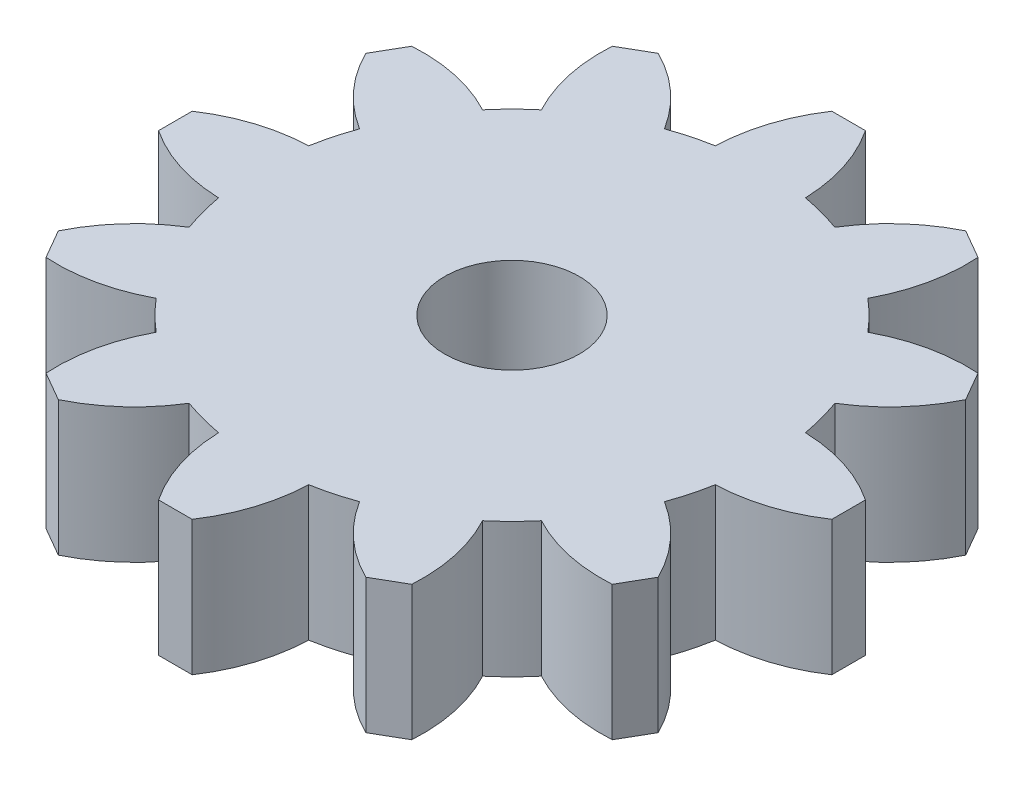
SolidWorks part; units mm, degrees
ref_plane "Front Plane" through (0, 0, 0) normal (0, 0, 1) x (1, 0, 0)
ref_plane "Top Plane" through (0, 0, 0) normal (0, 1, 0) x (1, 0, 0)
ref_plane "Right Plane" through (0, 0, 0) normal (1, 0, 0) x (0, 0, -1)
sketch "Sketch1" plane through (0, 0, 0) normal (0, 1, 0) x (1, 0, 0)
  line L0 (0, 0) -> (0, 18.9151) construction
  line L1 (-1, 20) -> (1, 20)
  line L2 (9.134, 17.8205) -> (10.866, 16.8205)
  line L3 (16.8205, 10.866) -> (17.8205, 9.134)
  line L4 (20, 1) -> (20, -1)
  line L5 (17.8205, -9.134) -> (16.8205, -10.866)
  line L6 (10.866, -16.8205) -> (9.134, -17.8205)
  line L7 (1, -20) -> (-1, -20)
  line L8 (-9.134, -17.8205) -> (-10.866, -16.8205)
  line L9 (-16.8205, -10.866) -> (-17.8205, -9.134)
  line L10 (-20, -1) -> (-20, 1)
  line L11 (-17.8205, 9.134) -> (-16.8205, 10.866)
  line L12 (-10.866, 16.8205) -> (-9.134, 17.8205)
  circle A0 centre (0, 0) radius 4
  arc A1 (-2.675, 14.7596) -> (-5.0632, 14.1196) centre (0, 0) ccw
  arc A2 (-1, 20) -> (-2.675, 14.7596) centre (7.3203, 14.4527) ccw
  arc A3 (1, 20) -> (2.675, 14.7596) centre (-7.3203, 14.4527) cw
  arc A4 (10.866, 16.8205) -> (9.6964, 11.4446) centre (0.8868, 16.1765) cw
  arc A5 (9.134, 17.8205) -> (5.0632, 14.1196) centre (13.5659, 8.8562) ccw
  arc A6 (17.8205, 9.134) -> (14.1196, 5.0632) centre (8.8562, 13.5659) cw
  arc A7 (16.8205, 10.866) -> (11.4446, 9.6964) centre (16.1765, 0.8868) ccw
  arc A8 (20, -1) -> (14.7596, -2.675) centre (14.4527, 7.3203) cw
  arc A9 (20, 1) -> (14.7596, 2.675) centre (14.4527, -7.3203) ccw
  arc A10 (16.8205, -10.866) -> (11.4446, -9.6964) centre (16.1765, -0.8868) cw
  arc A11 (17.8205, -9.134) -> (14.1196, -5.0632) centre (8.8562, -13.5659) ccw
  arc A12 (9.134, -17.8205) -> (5.0632, -14.1196) centre (13.5659, -8.8562) cw
  arc A13 (10.866, -16.8205) -> (9.6964, -11.4446) centre (0.8868, -16.1765) ccw
  arc A14 (-1, -20) -> (-2.675, -14.7596) centre (7.3203, -14.4527) cw
  arc A15 (1, -20) -> (2.675, -14.7596) centre (-7.3203, -14.4527) ccw
  arc A16 (-10.866, -16.8205) -> (-9.6964, -11.4446) centre (-0.8868, -16.1765) cw
  arc A17 (-9.134, -17.8205) -> (-5.0632, -14.1196) centre (-13.5659, -8.8562) ccw
  arc A18 (-17.8205, -9.134) -> (-14.1196, -5.0632) centre (-8.8562, -13.5659) cw
  arc A19 (-16.8205, -10.866) -> (-11.4446, -9.6964) centre (-16.1765, -0.8868) ccw
  arc A20 (-20, 1) -> (-14.7596, 2.675) centre (-14.4527, -7.3203) cw
  arc A21 (-20, -1) -> (-14.7596, -2.675) centre (-14.4527, 7.3203) ccw
  arc A22 (-16.8205, 10.866) -> (-11.4446, 9.6964) centre (-16.1765, 0.8868) cw
  arc A23 (-17.8205, 9.134) -> (-14.1196, 5.0632) centre (-8.8562, 13.5659) ccw
  arc A24 (-9.134, 17.8205) -> (-5.0632, 14.1196) centre (-13.5659, 8.8562) cw
  arc A25 (-10.866, 16.8205) -> (-9.6964, 11.4446) centre (-0.8868, 16.1765) ccw
  arc A26 (-9.6964, 11.4446) -> (-11.4446, 9.6964) centre (0, 0) ccw
  arc A27 (-14.1196, 5.0632) -> (-14.7596, 2.675) centre (0, 0) ccw
  arc A28 (-14.7596, -2.675) -> (-14.1196, -5.0632) centre (0, 0) ccw
  arc A29 (-11.4446, -9.6964) -> (-9.6964, -11.4446) centre (0, 0) ccw
  arc A30 (-5.0632, -14.1196) -> (-2.675, -14.7596) centre (0, 0) ccw
  arc A31 (2.675, -14.7596) -> (5.0632, -14.1196) centre (0, 0) ccw
  arc A32 (9.6964, -11.4446) -> (11.4446, -9.6964) centre (0, 0) ccw
  arc A33 (14.1196, -5.0632) -> (14.7596, -2.675) centre (0, 0) ccw
  arc A34 (14.7596, 2.675) -> (14.1196, 5.0632) centre (0, 0) ccw
  arc A35 (11.4446, 9.6964) -> (9.6964, 11.4446) centre (0, 0) ccw
  arc A36 (5.0632, 14.1196) -> (2.675, 14.7596) centre (0, 0) ccw
  point P80 (0, 0)
  dimension "D1" = 30
  dimension "D2" = 8
  dimension "D5" = 10
  dimension "D3" = 2
  dimension "D4" = 20
  dimension "D6" = 5.35
  dimension "D7" = 12
extrude "Boss-Extrude1" add sketch "Sketch1" along normal mid plane 8
